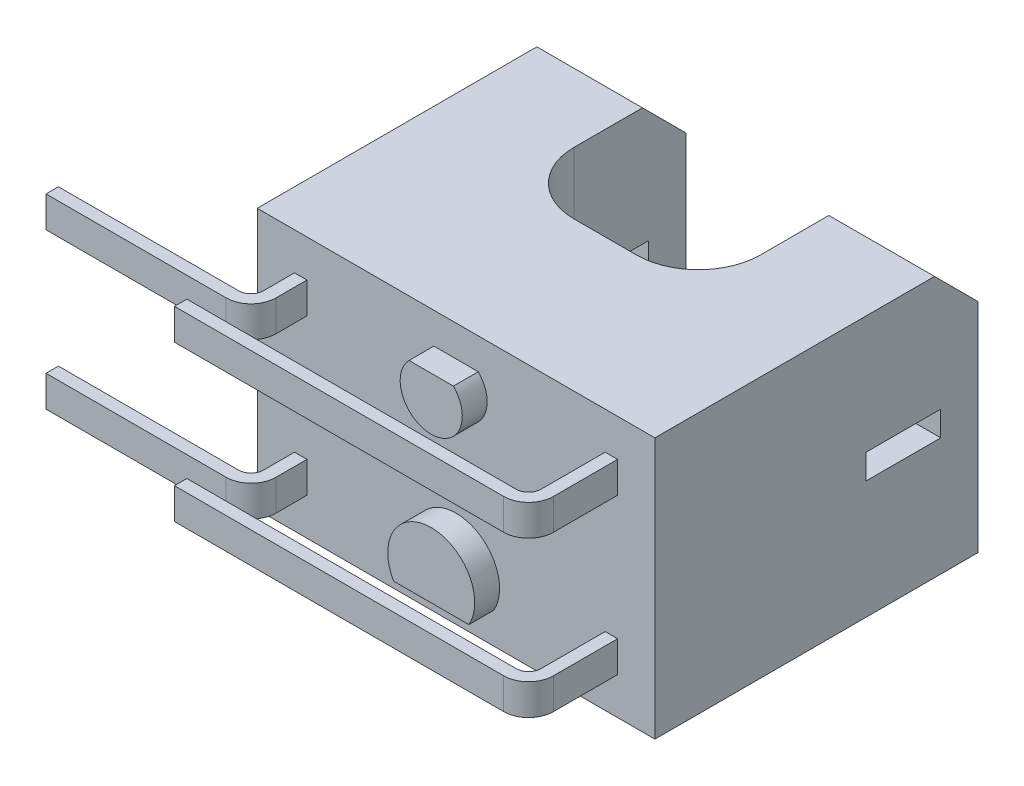
SolidWorks part; units mm, degrees
material "ПК/АБС"
ref_plane "Спереди" through (0, 0, 0) normal (0, 0, 1) x (1, 0, 0)
ref_plane "Сверху" through (0, 0, 0) normal (0, 1, 0) x (1, 0, 0)
ref_plane "Справа" through (0, 0, 0) normal (1, 0, 0) x (0, 0, -1)
sketch "Эскиз1" plane through (0, 0, 0) normal (0, 1, 0) x (1, 0, 0)
  line L0 (-3.2, 0) -> (-3.2, 5.2)
  line L1 (-3.2, 5.2) -> (-1.5, 5.2)
  line L2 (-1.5, 5.2) -> (-1.5, 3.4)
  line L4 (1.5, 3.4) -> (1.5, 5.2)
  line L5 (1.5, 5.2) -> (3.2, 5.2)
  line L6 (3.2, 5.2) -> (3.2, 0)
  line L7 (3.2, 0) -> (-3.2, 0)
  line L8 (-0.5, 2.4) -> (0.5, 2.4)
  arc A0 (-0.5, 2.4) -> (-1.5, 3.4) centre (-0.5, 3.4) cw
  arc A1 (1.5, 3.4) -> (0.5, 2.4) centre (0.5, 3.4) cw
  dimension "D1" = 1
  dimension "D3" = 3
  dimension "D4" = 2.8
  dimension "D5" = 6.4
  dimension "D6" = 5.2
extrude "Бобышка-Вытянуть1" add sketch "Эскиз1" along normal blind 4.2
chamfer "Фаска1" distance 0.7 angle 45 2 edges at (2.35, 4.2, -5.2) (-2.35, 4.2, -5.2)
sketch "Эскиз2" plane through (-3.2, 0, 0) normal (-1, 0, 0) x (0, 0, 1)
  line L0 (-4.6, 1.9) -> (-3.4, 2.3) construction
  line L1 (-4.6, 1.9) -> (-3.4, 1.9)
  line L2 (-4.6, 1.9) -> (-4.6, 2.3)
  line L3 (-4.6, 2.3) -> (-3.4, 2.3)
  line L4 (-3.4, 1.9) -> (-3.4, 2.3)
  line L5 (-4.6, 2.3) -> (-3.4, 1.9) construction
  line L6 (-5.2, 3.5) -> (-5.2, 0) construction
  line L7 (0, 4.2) -> (0, 0) construction
  point P4 (-4, 2.1)
  point P7 (0, 2.1)
  dimension "D1" = 0.4
  dimension "D2" = 1.2
  dimension "D3" = 1.2
extrude "Вырез-Вытянуть1" cut sketch "Эскиз2" against normal through all
sketch "Эскиз3" plane through (0, 0, 0) normal (0, 0, 1) x (1, 0, 0)
  line L0 (0, 4.2) -> (0, 0) construction
  line L2 (-0.3571, 3.7) -> (0.3571, 3.7)
  line L3 (-0.6062, 0.5) -> (0.6062, 0.5)
  line L4 (-2.5, 0.85) -> (2.5, 3.35) construction
  line L5 (-2.6, 3.1) -> (-2.4, 3.1)
  line L6 (-2.6, 3.1) -> (-2.6, 3.6)
  line L7 (-2.6, 3.6) -> (-2.4, 3.6)
  line L8 (-2.4, 3.1) -> (-2.4, 3.6)
  line L9 (-2.6, 3.1) -> (-2.4, 3.6) construction
  line L10 (-2.6, 3.6) -> (-2.4, 3.1) construction
  line L11 (2.4, 3.1) -> (2.6, 3.1)
  line L12 (2.4, 3.1) -> (2.4, 3.6)
  line L13 (2.4, 3.6) -> (2.6, 3.6)
  line L14 (2.6, 3.1) -> (2.6, 3.6)
  line L15 (2.4, 3.1) -> (2.6, 3.6) construction
  line L16 (2.4, 3.6) -> (2.6, 3.1) construction
  line L17 (2.4, 0.6) -> (2.6, 0.6)
  line L18 (2.4, 0.6) -> (2.4, 1.1)
  line L19 (2.4, 1.1) -> (2.6, 1.1)
  line L20 (2.6, 0.6) -> (2.6, 1.1)
  line L21 (2.4, 0.6) -> (2.6, 1.1) construction
  line L22 (2.4, 1.1) -> (2.6, 0.6) construction
  line L23 (-2.6, 0.6) -> (-2.4, 0.6)
  line L24 (-2.6, 0.6) -> (-2.6, 1.1)
  line L25 (-2.6, 1.1) -> (-2.4, 1.1)
  line L26 (-2.4, 0.6) -> (-2.4, 1.1)
  line L27 (-2.6, 0.6) -> (-2.4, 1.1) construction
  line L28 (-2.6, 1.1) -> (-2.4, 0.6) construction
  line L29 (2.5, 0.85) -> (-2.5, 3.35) construction
  arc A0 (0.3571, 3.7) -> (-0.3571, 3.7) centre (0, 3.35) cw
  arc A1 (-0.6062, 0.5) -> (0.6062, 0.5) centre (0, 0.85) cw
  point P9 (0, 3.7)
  point P10 (0, 0.5)
  point P13 (-2.5, 3.35)
  point P18 (2.5, 3.35)
  point P23 (2.5, 0.85)
  point P28 (-2.5, 0.85)
  point P37 (0, 2.1)
  point P38 (0, 2.1)
  dimension "D1" = 0.5
  dimension "D2" = 0.2
  dimension "D3" = 0.5
extrude "Бобышка-Вытянуть2" add sketch "Эскиз3" along normal blind 0.4
sketch "Эскиз4" plane through (0, 0, 0.4) normal (0, 0, 1) x (1, 0, 0)
  line L0 (2.6, 3.6) -> (2.6, 3.1)
  line L1 (2.6, 3.1) -> (2.4, 3.1)
  line L3 (2.4, 3.1) -> (2.4, 3.6)
  line L4 (2.4, 3.6) -> (2.6, 3.6)
  line L5 (2.4, 1.1) -> (2.6, 1.1)
  line L6 (2.6, 1.1) -> (2.6, 0.6)
  line L7 (2.6, 0.6) -> (2.4, 0.6)
  line L8 (2.4, 0.6) -> (2.4, 1.1)
sketch3d "Трехмерный эскиз1"
  line L0 (2.4, 3.1, 0.4) -> (2.4, 3.1, 1.0333)
  line L1 (2.2, 3.1, 1.2333) -> (-3.1, 3.1, 1.2333)
  arc A0 (2.2, 3.1, 1.2333) -> (2.4, 3.1, 1.0333) centre (2.2, 3.1, 1.0333) ccw
  point P6 (2.4, 3.1, 1.2333)
  point P7 (2.2, 3.3, 1.0333)
  dimension "D1" = 0.2
  dimension "D2" = 5.5
sweep "По траектории1" add profiles "Эскиз4" path "Трехмерный эскиз1"
sketch "Эскиз5" plane through (0, 0, 0.4) normal (0, 0, 1) x (1, 0, 0)
  line L0 (-2.4, 3.6) -> (-2.4, 3.1)
  line L1 (-2.4, 3.1) -> (-2.6, 3.1)
  line L2 (-2.6, 3.1) -> (-2.6, 3.6)
  line L3 (-2.6, 3.6) -> (-2.4, 3.6)
  line L4 (-2.6, 1.1) -> (-2.4, 1.1)
  line L5 (-2.4, 1.1) -> (-2.4, 0.6)
  line L6 (-2.4, 0.6) -> (-2.6, 0.6)
  line L7 (-2.6, 0.6) -> (-2.6, 1.1)
sketch3d "Трехмерный эскиз2"
  line L0 (-2.6, 0.6, 0.4) -> (-2.6, 0.6, 0.5)
  line L1 (-2.8, 0.6, 0.7) -> (-5.7, 0.6, 0.7)
  arc A0 (-2.8, 0.6, 0.7) -> (-2.6, 0.6, 0.5) centre (-2.8, 0.6, 0.5) ccw
  point P6 (-2.6, 0.6, 0.7)
  point P7 (-2.8, 0.8, 0.5)
  dimension "D1" = 0.2
  dimension "D2" = 2.5
  dimension "D3" = 0.7
sweep "По траектории2" add profiles "Эскиз5" path "Трехмерный эскиз2"
